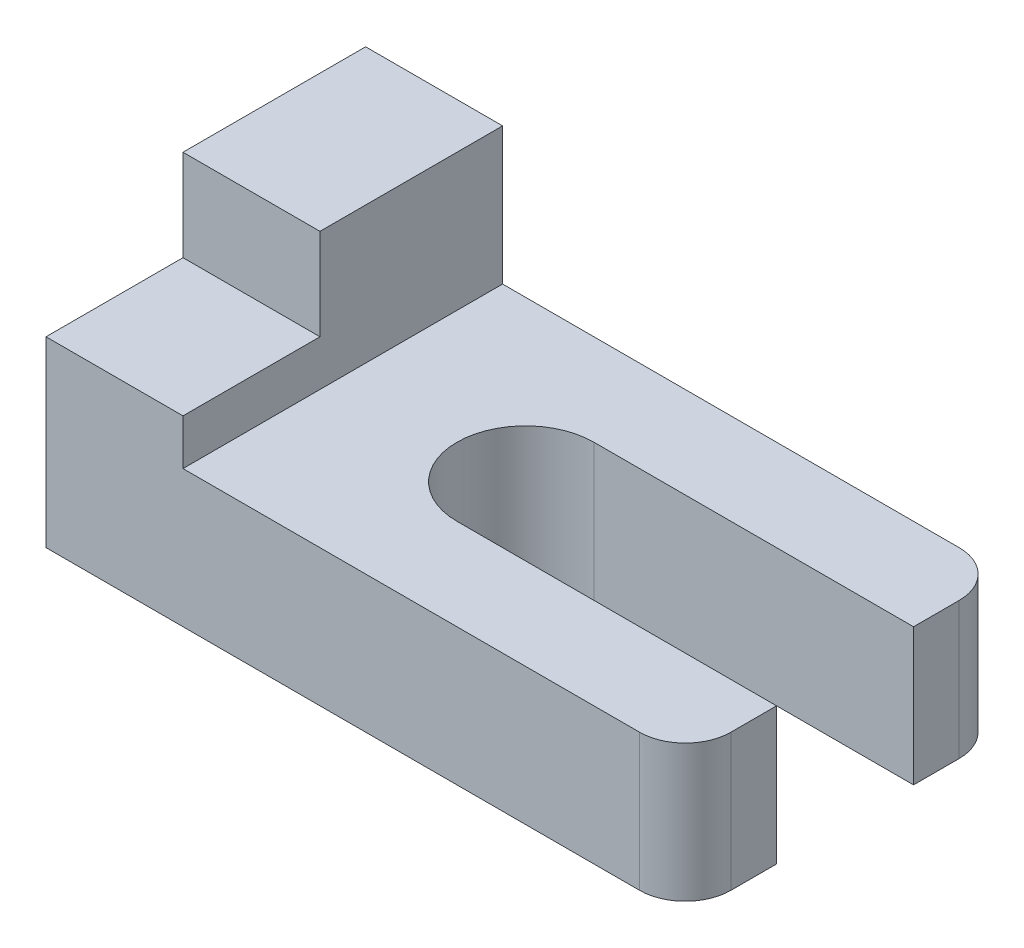
SolidWorks part; units mm, degrees
ref_plane "Front Plane" through (0, 0, 0) normal (0, 0, 1) x (1, 0, 0)
ref_plane "Top Plane" through (0, 0, 0) normal (0, 1, 0) x (1, 0, 0)
ref_plane "Right Plane" through (0, 0, 0) normal (1, 0, 0) x (0, 0, -1)
sketch "Sketch1" plane through (0, 0, 0) normal (0, 1, 0) x (1, 0, 0)
  line L1 (0, 0) -> (70, 0)
  line L2 (0, 0) -> (0, 35)
  line L3 (0, 35) -> (70, 35)
  line L4 (70, 0) -> (70, 35)
  dimension "D1" = 70
  dimension "D2" = 35
extrude "Boss-Extrude1" add sketch "Sketch1" along normal blind 30
sketch "Sketch2" plane through (0, 30, 0) normal (0, 1, 0) x (1, 0, 0)
  line L0 (0, 35) -> (15, 35) construction
  line L1 (70, 35) -> (0, 35) construction
  line L3 (15, 35) -> (70, 35)
  line L4 (15, 35) -> (15, 0)
  line L5 (15, 0) -> (70, 0)
  line L6 (70, 35) -> (70, 0)
  dimension "D1" = 15
extrude "Cut-Extrude1" cut sketch "Sketch2" against normal blind 15
sketch "Sketch3" plane through (0, 30, 0) normal (0, 1, 0) x (1, 0, 0)
  line L0 (15, 35) -> (15, 0) construction
  line L1 (0, 0) -> (15, 0)
  line L2 (0, 0) -> (0, 15)
  line L3 (0, 15) -> (15, 15)
  line L4 (15, 0) -> (15, 15)
  dimension "D1" = 15
  dimension "D2" = 15
extrude "Cut-Extrude2" cut sketch "Sketch3" against normal blind 10
fillet "Fillet1" radius 5 2 edges at (70, 7.5, -35) (70, 7.5, 0)
sketch "Sketch4" plane through (0, 15, 0) normal (0, 1, 0) x (1, 0, 0)
  line L0 (70, 5) -> (70, 10) construction
  line L1 (70, 5) -> (70, 30) construction
  line L2 (70, 30) -> (70, 25) construction
  line L4 (70, 25) -> (35, 25)
  line L5 (70, 25) -> (70, 10)
  line L6 (70, 10) -> (35, 10)
  line L7 (35, 25) -> (35, 10)
  dimension "D1" = 5
  dimension "D2" = 5
  dimension "D3" = 35
extrude "Cut-Extrude3" cut sketch "Sketch4" against normal through all
sketch "Sketch5" plane through (0, 15, 0) normal (0, 1, 0) x (1, 0, 0)
  line L0 (35, 25) -> (35, 17.5) construction
  line L1 (35, 25) -> (35, 10) construction
  circle A0 centre (35, 17.5) radius 7.5
extrude "Cut-Extrude4" cut sketch "Sketch5" against normal through all
